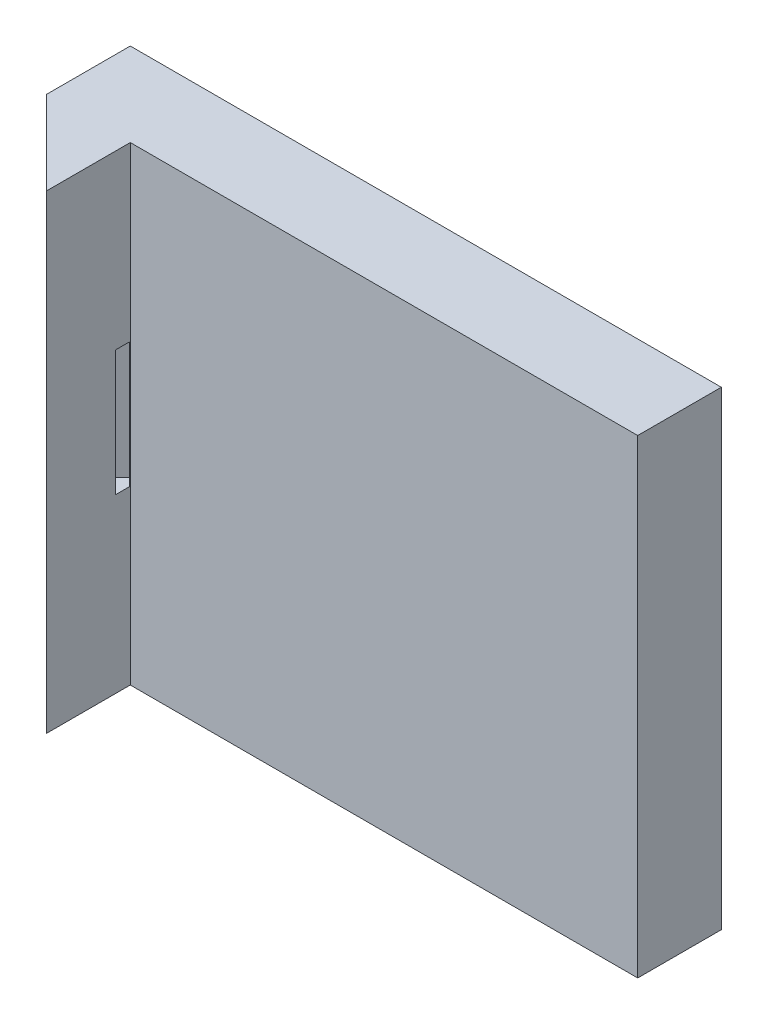
SolidWorks part; units mm, degrees
ref_plane "Front Plane" through (0, 0, 0) normal (0, 0, 1) x (1, 0, 0)
ref_plane "Top Plane" through (0, 0, 0) normal (0, 1, 0) x (1, 0, 0)
ref_plane "Right Plane" through (0, 0, 0) normal (1, 0, 0) x (0, 0, -1)
sketch "Sketch1" plane through (0, 0, 0) normal (0, 0, 1) x (1, 0, 0)
  line L1 (-175, -28.1) -> (175, -28.1)
  line L2 (-175, -28.1) -> (-175, 28.1)
  line L3 (-175, 28.1) -> (175, 28.1)
  line L4 (175, -28.1) -> (175, 28.1)
  line L5 (-175, -28.1) -> (175, 28.1) construction
  line L6 (-175, 28.1) -> (175, -28.1) construction
  point P0 (0, 0)
extrude "Boss-Extrude1" add sketch "Sketch1" along normal blind 10
sketch "Sketch2" plane through (0, 0, 10) normal (0, 0, 1) x (1, 0, 0)
  line L2 (175, 28.1) -> (-175, 28.1) construction
  line L3 (-28.1, -28.1) -> (28.1, -28.1)
  line L4 (-28.1, -28.1) -> (-28.1, 28.1)
  line L5 (-28.1, 28.1) -> (28.1, 28.1)
  line L6 (28.1, -28.1) -> (28.1, 28.1)
  point P8 (0, 0)
extrude "Cut-Extrude1" cut sketch "Sketch2" against normal blind 5
sketch "Sketch3" plane through (175, 0, 0) normal (1, 0, 0) x (0, 0, -1)
  line L1 (-10, 28.1) -> (0, 28.1)
  line L2 (-10, 28.1) -> (-10, -28.1)
  line L3 (-10, -28.1) -> (0, -28.1)
  line L4 (0, 28.1) -> (0, -28.1)
extrude "Boss-Extrude2" add sketch "Sketch3" along normal blind 10
sketch "Sketch4" plane through (0, 0, 10) normal (0, 0, 1) x (1, 0, 0)
  line L0 (28.1, -28.1) -> (185, -28.1) construction
  line L1 (185, 28.1) -> (175, 28.1)
  line L2 (185, 28.1) -> (185, -28.1)
  line L3 (185, -28.1) -> (175, -28.1)
  line L4 (175, 28.1) -> (175, -28.1)
extrude "Boss-Extrude3" add sketch "Sketch4" along normal blind 10
sketch "Sketch5" plane through (0, 28.1, 0) normal (0, 1, 0) x (1, 0, 0)
  line L0 (175, -20) -> (185, -10)
  line L1 (185, 0) -> (185, -20) construction
  line L2 (185, -10) -> (185, -20)
  line L3 (185, -20) -> (175, -20)
extrude "Cut-Extrude2" cut sketch "Sketch5" against normal blind 56.2
sketch "Sketch6" plane through (-175, 0, 0) normal (-1, 0, 0) x (0, 0, 1)
  line L1 (0, -28.1) -> (10, -28.1)
  line L2 (0, -28.1) -> (0, 28.1)
  line L3 (0, 28.1) -> (10, 28.1)
  line L4 (10, -28.1) -> (10, 28.1)
extrude "Boss-Extrude4" add sketch "Sketch6" along normal blind 10
sketch "Sketch7" plane through (0, 0, 10) normal (0, 0, 1) x (1, 0, 0)
  line L0 (-28.1, 28.1) -> (-185, 28.1) construction
  line L1 (-185, -28.1) -> (-175, -28.1)
  line L2 (-185, -28.1) -> (-185, 28.1)
  line L3 (-185, 28.1) -> (-175, 28.1)
  line L4 (-175, -28.1) -> (-175, 28.1)
extrude "Boss-Extrude5" add sketch "Sketch7" along normal blind 10
sketch "Sketch8" plane through (0, 28.1, 0) normal (0, 1, 0) x (1, 0, 0)
  line L0 (-175, -20) -> (-185, -10)
  line L1 (-185, -20) -> (-185, 0) construction
  line L2 (-185, -10) -> (-185, -20)
  line L3 (-185, -20) -> (-175, -20)
extrude "Cut-Extrude3" cut sketch "Sketch8" against normal blind 56.2
sketch "Sketch9" plane through (0, 0, 5) normal (0, 0, 1) x (1, 0, 0)
  line L3 (-15, -15) -> (15, -15)
  line L4 (-15, -15) -> (-15, 15)
  line L5 (-15, 15) -> (15, 15)
  line L6 (15, -15) -> (15, 15)
  point P4 (0, 0)
extrude "Cut-Extrude4" cut sketch "Sketch9" against normal blind 5
sketch "Sketch10" plane through (0, 0, 5) normal (0, 0, 1) x (1, 0, 0)
  circle A2 centre (21.55, 21.55) radius 3
  circle A3 centre (-21.55, -21.55) radius 3
  circle A4 centre (-21.55, 21.55) radius 3
  circle A5 centre (21.55, -21.55) radius 3
extrude "Cut-Extrude5" cut sketch "Sketch10" against normal blind 5
sketch "Sketch11" plane through (97.5, 0, 97.5) normal (0.7071, 0, 0.7071) x (0.7071, 0, -0.7071)
  line L3 (117.9226, -7.5) -> (115.4226, -7.5)
  line L4 (117.9226, -7.5) -> (117.9226, 7.5)
  line L5 (117.9226, 7.5) -> (115.4226, 7.5)
  line L6 (115.4226, -7.5) -> (115.4226, 7.5)
  line L7 (117.9226, -7.5) -> (115.4226, 7.5) construction
  line L8 (117.9226, 7.5) -> (115.4226, -7.5) construction
  point P6 (116.6726, 0)
extrude "Cut-Extrude6" cut sketch "Sketch11" against normal blind 7
sketch "Sketch12" plane through (-97.5, 0, 97.5) normal (-0.7071, 0, 0.7071) x (0.7071, 0, 0.7071)
  line L2 (-117.9226, 7.5) -> (-115.4226, 7.5)
  line L3 (-117.9226, 7.5) -> (-117.9226, -7.5)
  line L4 (-117.9226, -7.5) -> (-115.4226, -7.5)
  line L5 (-115.4226, 7.5) -> (-115.4226, -7.5)
  line L6 (-117.9226, 7.5) -> (-115.4226, -7.5) construction
  line L7 (-117.9226, -7.5) -> (-115.4226, 7.5) construction
  point P4 (-116.6726, 0)
extrude "Cut-Extrude7" cut sketch "Sketch12" against normal blind 7
sketch "Sketch14" plane through (0, 0, 10) normal (0, 0, 1) x (1, 0, 0)
  line L0 (-175, -28.1) -> (-28.1, -28.1) construction
  line L6 (-94.3, 28.1) -> (185, 28.1)
  line L7 (-94.3, 28.1) -> (-94.3, -28.1)
  line L8 (-94.3, -28.1) -> (185, -28.1)
  line L9 (185, 28.1) -> (185, -28.1)
extrude "Cut-Extrude10" cut sketch "Sketch14" against normal blind 10
sketch "Sketch15" plane through (0, 0, 10) normal (0, 0, 1) x (1, 0, 0)
  line L0 (-175, -28.1) -> (-94.3, -28.1) construction
  line L1 (-94.3, 28.1) -> (-114.3, 28.1)
  line L2 (-94.3, 28.1) -> (-94.3, -28.1)
  line L3 (-94.3, -28.1) -> (-114.3, -28.1)
  line L4 (-114.3, 28.1) -> (-114.3, -28.1)
extrude "Cut-Extrude11" cut sketch "Sketch15" against normal blind 10
